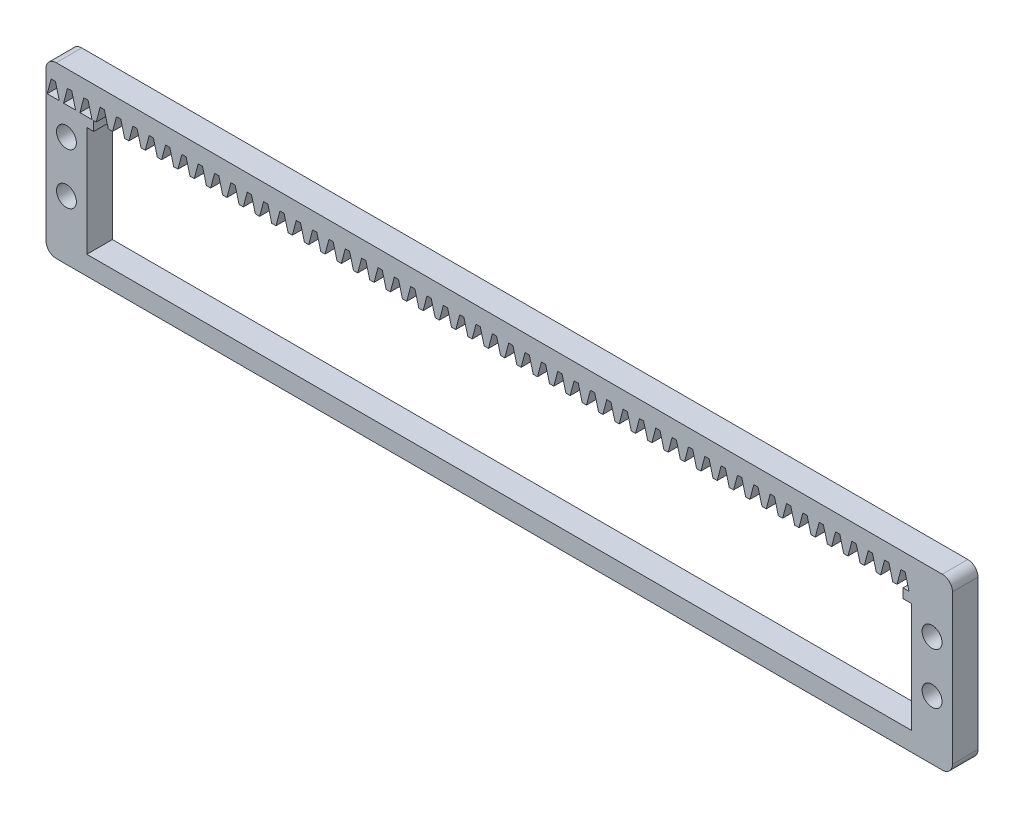
SolidWorks part; units mm, degrees
other "Markup1"
sketch "Sketch6" plane through (0, -30, 3.6) normal (0, 0, 1) x (1, 0, 0)
other "Markup2"
sketch "Sketch7" plane through (0, -30, 3.6) normal (0, 0, 1) x (1, 0, 0)
ref_plane "Front Plane" through (0, 0, 0) normal (0, 0, 1) x (1, 0, 0)
ref_plane "Top Plane" through (0, 0, 0) normal (0, 1, 0) x (1, 0, 0)
ref_plane "Right Plane" through (0, 0, 0) normal (1, 0, 0) x (0, 0, -1)
sketch "Sketch1" plane through (0, 0, 0) normal (0, 0, 1) x (1, 0, 0)
  line L1 (2, 0) -> (175.5, 0)
  line L2 (0, -2) -> (0, -31.22)
  line L3 (2, -33.22) -> (175.5, -33.22)
  line L4 (177.5, -2) -> (177.5, -31.22)
  arc A0 (175.5, -33.22) -> (177.5, -31.22) centre (175.5, -31.22) ccw
  arc A1 (0, -31.22) -> (2, -33.22) centre (2, -31.22) ccw
  arc A2 (2, 0) -> (0, -2) centre (2, -2) ccw
  arc A3 (175.5, 0) -> (177.5, -2) centre (175.5, -2) cw
  point P7 (177.5, -33.22)
  point P12 (0, 0)
  point P15 (177.5, 0)
  dimension "D3" = 2
  dimension "D1" = 33.22
  dimension "D2" = 177.5
extrude "Boss-Extrude1" add sketch "Sketch1" along normal blind 5
sketch "Sketch2" plane through (0, 0, 5) normal (0, 0, 1) x (1, 0, 0)
  line L0 (2, -33.22) -> (175.5, -33.22) construction
  line L1 (8, -8) -> (169.5, -8)
  line L2 (8, -8) -> (8, -29.5)
  line L3 (8, -29.5) -> (169.5, -29.5)
  line L4 (169.5, -8) -> (169.5, -29.5)
  line L5 (0, -2) -> (0, -31.22) construction
  line L7 (177.5, -31.22) -> (177.5, -2) construction
  line L8 (8, -18.75) -> (169.5, -18.75) construction
  line L12 (8, -29.5) -> (169.5, -29.5) construction
  line L13 (169.5, -4.3144) -> (169.5, -29.5) construction
  dimension "D1" = 21.5
  dimension "D2" = 8
  dimension "D3" = 8
  dimension "D4" = 3.72
extrude "Cut-Extrude1" cut sketch "Sketch2" against normal through all
sketch "Sketch3" plane through (0, 0, 5) normal (0, 0, 1) x (1, 0, 0)
  line L0 (169.5, -8) -> (8, -8) construction
  line L1 (9.35, -8) -> (167.82, -8)
  line L2 (9.35, -8) -> (9.35, -6.15)
  line L3 (9.35, -6.15) -> (167.82, -6.15)
  line L4 (167.82, -8) -> (167.82, -6.15)
  line L5 (169.5, -29.5) -> (169.5, -8) construction
  line L6 (8, -8) -> (8, -29.5) construction
  dimension "D1" = 1.85
  dimension "D2" = 1.68
  dimension "D3" = 1.35
extrude "Cut-Extrude2" cut sketch "Sketch3" against normal through all
sketch "Sketch4" plane through (0, 0, 5) normal (0, 0, 1) x (1, 0, 0)
  line L0 (170.2, -6.15) -> (169, -6.15) construction
  line L1 (167.82, -6.15) -> (9.35, -6.15) construction
  line L2 (170.2, -6.15) -> (170.965, -3.2492) construction
  line L3 (170.965, -3.2492) -> (168.235, -3.2492) construction
  line L4 (168.235, -3.2492) -> (169, -6.15)
  line L5 (168.235, -3.2492) -> (167.405, -3.2492)
  line L6 (167.405, -3.2492) -> (166.64, -6.15)
  line L7 (166.64, -6.15) -> (169, -6.15)
  line L10 (169, -6.15) -> (170.2, -6.15) construction
  dimension "D1" = 1.2
  dimension "D3" = 3
  dimension "D4" = 0.83
  dimension "D5" = 2.73
extrude "Cut-Extrude4" cut sketch "Sketch4" against normal through all
pattern_linear "LPattern1" count 55 spacing 3.2 along (-1, 0, 0) of "Cut-Extrude4"
sketch "Sketch5" plane through (0, 0, 5) normal (0, 0, 1) x (1, 0, 0)
  line L0 (169.5, -16.61) -> (177.5, -16.61) construction
  line L1 (175.5, 0) -> (2, 0) construction
  line L2 (8, -8) -> (8, -29.5) construction
  line L3 (0, -2) -> (0, -31.22) construction
  line L4 (2, -33.22) -> (175.5, -33.22) construction
  line L5 (0, -16.61) -> (8, -16.61) construction
  line L7 (173.5, -11.61) -> (173.5, -21.61) construction
  line L8 (4, -11.61) -> (4, -21.61) construction
  line L9 (169.5, -29.5) -> (169.5, -8) construction
  line L10 (177.5, -31.22) -> (177.5, -2) construction
  circle A4 centre (4, -11.61) radius 1.95
  circle A5 centre (4, -21.61) radius 1.95
  circle A6 centre (173.5, -11.61) radius 1.95
  circle A7 centre (173.5, -21.61) radius 1.95
  point P8 (173.5, -16.61)
  point P18 (4, -16.61)
  point P22 (4, -16.61)
  point P31 (173.5, -16.61)
  dimension "D1" = 3.9
  dimension "D3" = 3.9
  dimension "D4" = 3.9
  dimension "D6" = 3.9
  dimension "D5" = 10
  dimension "D7" = 10
extrude "Cut-Extrude5" cut sketch "Sketch5" against normal blind 10
